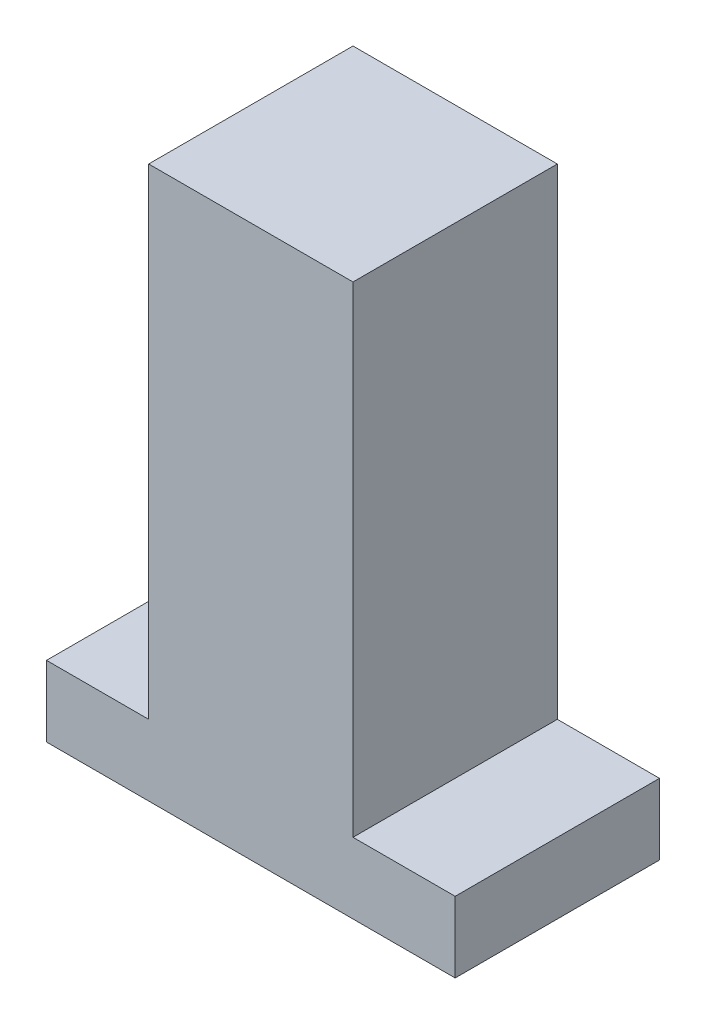
SolidWorks part; units mm, degrees
ref_plane "Front Plane" through (0, 0, 0) normal (0, 0, 1) x (1, 0, 0)
ref_plane "Top Plane" through (0, 0, 0) normal (0, 1, 0) x (1, 0, 0)
ref_plane "Right Plane" through (0, 0, 0) normal (1, 0, 0) x (0, 0, -1)
sketch "Sketch1" plane through (0, 0, 0) normal (0, 0, 1) x (1, 0, 0)
  line L0 (0, -81) -> (-15, -81)
  line L1 (0, 0) -> (30, 0)
  line L2 (0, 0) -> (0, -70.6105)
  line L3 (0, -81) -> (30, -81)
  line L4 (30, 0) -> (30, -70.6105)
  line L6 (45, -81) -> (45, -70.6105)
  line L7 (45, -70.6105) -> (30, -70.6105)
  line L8 (-15, -81) -> (-15, -70.6105)
  line L9 (0, -70.6105) -> (-15, -70.6105)
  line L11 (-15, -81) -> (45, -81)
  point P5 (15, -81)
  dimension "D1" = 81
  dimension "D2" = 30
extrude "Boss-Extrude1" add sketch "Sketch1" along normal blind 30 contours L3 L11 L6 L7 L4 L1 L2 L9 L8 L0
